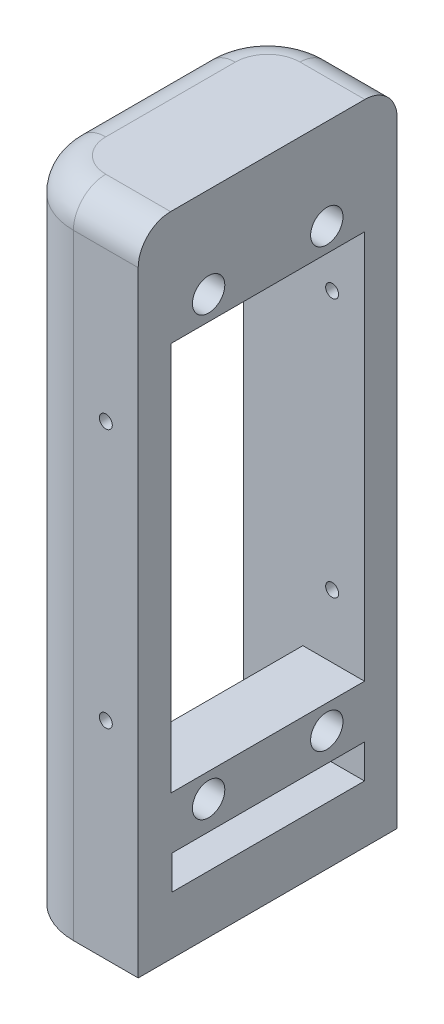
SolidWorks part; units mm, degrees
ref_plane "Front Plane" through (0, 0, 0) normal (0, 0, 1) x (1, 0, 0)
ref_plane "Top Plane" through (0, 0, 0) normal (0, 1, 0) x (1, 0, 0)
ref_plane "Right Plane" through (0, 0, 0) normal (1, 0, 0) x (0, 0, -1)
sketch "Sketch1" plane through (0, 0, 0) normal (0, 1, 0) x (1, 0, 0)
  line L0 (5.9548, -0.4092) -> (5.9548, -20.4092)
  line L1 (-14.0452, 9.5908) -> (-14.0452, -10.4092)
  line L2 (5.9548, 19.5908) -> (5.9548, -0.4092)
  line L3 (-14.0452, 9.5908) -> (-14.0452, -0.4092)
  line L4 (-4.0452, 19.5908) -> (5.9548, 19.5908)
  line L5 (-4.0452, -20.4092) -> (5.9548, -20.4092)
  arc A0 (-14.0452, -10.4092) -> (-4.0452, -20.4092) centre (-4.0452, -10.4092) ccw
  arc A1 (-4.0452, 19.5908) -> (-14.0452, 9.5908) centre (-4.0452, 9.5908) ccw
  point P2 (15.9548, -0.4092)
extrude "Boss-Extrude1" add sketch "Sketch1" along normal blind 100 contours L4 A1 L1 A0 L5 L0 L2
sketch "Sketch12" plane through (0, 100, 0) normal (0, 1, 0) x (1, 0, 0)
  line L0 (5.9548, -0.4092) -> (-2.8452, -0.4092) construction
  line L1 (5.9548, 19.5908) -> (5.9548, -20.4092) construction
  line L2 (-2.8452, -0.4092) -> (-14.0452, -0.4092) construction
  line L3 (-14.0452, 9.5908) -> (-14.0452, -10.4092) construction
  dimension "D1" = 8.8
sketch "Sketch11" plane through (-14.0452, 0, 0) normal (-1, 0, 0) x (0, 0, 1)
  line L7 (-14.1408, 22.615) -> (-14.1408, 14.5)
  line L8 (-14.1408, 14.5) -> (-10.1408, 14.5)
  line L9 (-10.1408, 14.5) -> (-10.1408, 16.148)
  line L11 (-7.2908, 14.5) -> (8.1092, 14.5)
  line L14 (10.9592, 14.5) -> (14.9592, 14.5)
  line L15 (14.9592, 14.5) -> (14.9592, 22.615)
  line L20 (14.9592, 81.925) -> (14.9592, 90)
  line L21 (14.9592, 90) -> (10.9592, 90)
  line L24 (8.1092, 90) -> (-7.2908, 90)
  line L27 (-10.1408, 90) -> (-14.1408, 90)
  line L28 (-14.1408, 90) -> (-14.1408, 81.925)
  line L32 (-14.1408, 81.925) -> (-14.1408, 80.015)
  line L33 (14.9592, 80.015) -> (14.9592, 81.925)
  line L35 (-14.1408, 38.515) -> (-14.1408, 22.615)
  line L37 (14.9592, 22.615) -> (14.9592, 38.515)
  line L42 (-14.1408, 80.015) -> (-14.1408, 38.515)
  line L46 (14.9592, 38.515) -> (14.9592, 80.015)
  line L47 (0.4092, 100) -> (0.4092, 90) construction
  line L48 (-9.5908, 100) -> (10.4092, 100) construction
  line L49 (-9.5908, 0) -> (10.4092, 0) construction
  line L50 (0.4092, 100) -> (0.4092, 90)
  line L51 (14.9592, 90) -> (-14.1408, 90)
  line L52 (14.9592, 90) -> (14.9592, 14.5)
  line L53 (-14.1408, 90) -> (-14.1408, 14.5)
  line L54 (14.9592, 14.5) -> (-14.1408, 14.5)
  line L56 (0.4092, 14.5) -> (0.4092, 0) construction
  dimension "D1" = 10
extrude "Cut-Extrude1" cut sketch "Sketch11" against normal blind 11.2
sketch "Sketch13" plane through (-2.8452, 0, 0) normal (-1, 0, 0) x (0, 0, 1)
  line L0 (14.9592, 22.615) -> (4.2292, 22.615)
  line L1 (4.2292, 22.615) -> (4.2292, 19.65)
  line L2 (2.5592, 19.65) -> (2.5592, 22.615)
  line L3 (2.5592, 22.615) -> (-1.7408, 22.615)
  line L4 (-1.7408, 22.615) -> (-1.7408, 19.65)
  line L5 (-3.4108, 19.65) -> (-3.4108, 22.615)
  line L6 (-3.4108, 22.615) -> (-14.1408, 22.615)
  line L7 (-14.1408, 22.615) -> (-14.1408, 14.5)
  line L8 (-14.1408, 14.5) -> (-10.1408, 14.5)
  line L9 (-10.1408, 14.5) -> (-10.1408, 16.148)
  line L10 (-7.2908, 16.148) -> (-7.2908, 14.5)
  line L11 (-7.2908, 14.5) -> (8.1092, 14.5)
  line L12 (8.1092, 14.5) -> (8.1092, 16.148)
  line L13 (10.9592, 16.148) -> (10.9592, 14.5)
  line L14 (10.9592, 14.5) -> (14.9592, 14.5)
  line L15 (14.9592, 14.5) -> (14.9592, 22.615)
  line L16 (-1.7408, 81.925) -> (2.5592, 81.925)
  line L17 (2.5592, 81.925) -> (2.5592, 84.85)
  line L18 (4.2292, 84.85) -> (4.2292, 81.925)
  line L19 (4.2292, 81.925) -> (14.9592, 81.925)
  line L20 (14.9592, 81.925) -> (14.9592, 90)
  line L21 (14.9592, 90) -> (10.9592, 90)
  line L22 (10.9592, 90) -> (10.9592, 88.352)
  line L23 (8.1092, 88.352) -> (8.1092, 90)
  line L24 (8.1092, 90) -> (-7.2908, 90)
  line L25 (-7.2908, 90) -> (-7.2908, 88.352)
  line L26 (-10.1408, 88.352) -> (-10.1408, 90)
  line L27 (-10.1408, 90) -> (-14.1408, 90)
  line L28 (-14.1408, 90) -> (-14.1408, 81.925)
  line L29 (-14.1408, 81.925) -> (-3.4108, 81.925)
  line L30 (-3.4108, 81.925) -> (-3.4108, 84.85)
  line L31 (-1.7408, 84.85) -> (-1.7408, 81.925)
  line L32 (-14.1408, 81.925) -> (-14.1408, 80.015)
  line L33 (14.9592, 80.015) -> (14.9592, 81.925)
  line L34 (14.9592, 81.925) -> (-14.1408, 81.925)
  line L35 (-14.1408, 38.515) -> (-14.1408, 22.615)
  line L36 (-14.1408, 22.615) -> (14.9592, 22.615)
  line L37 (14.9592, 22.615) -> (14.9592, 38.515)
  line L38 (12.9842, 38.515) -> (12.9842, 24.115)
  line L39 (12.9842, 24.115) -> (-12.1658, 24.115)
  line L40 (-12.1658, 24.115) -> (-12.1658, 38.515)
  line L41 (6.3592, 46.155) -> (-5.5408, 46.155)
  line L42 (-14.1408, 80.015) -> (-14.1408, 38.515)
  line L43 (-12.1658, 38.515) -> (-12.1658, 43.815)
  line L44 (-12.1658, 43.815) -> (12.9842, 43.815)
  line L45 (12.9842, 43.815) -> (12.9842, 38.515)
  line L46 (14.9592, 38.515) -> (14.9592, 80.015)
  line L51 (-14.1408, 14.5) -> (14.9592, 14.5)
  line L52 (14.9592, 14.5) -> (14.9592, 90)
  line L53 (14.9592, 90) -> (-14.1408, 90)
  line L54 (-14.1408, 90) -> (-14.1408, 14.5)
  line L55 (-14.1408, 14.5) -> (14.9592, 14.5)
  line L56 (14.9592, 14.5) -> (14.9592, 90)
  line L57 (14.9592, 90) -> (-14.1408, 90)
  line L58 (-14.1408, 90) -> (-14.1408, 14.5)
  arc A0 (2.5592, 19.65) -> (4.2292, 19.65) centre (3.3942, 19.65) ccw
  arc A1 (-3.4108, 19.65) -> (-1.7408, 19.65) centre (-2.5758, 19.65) ccw
  arc A2 (-7.2908, 16.148) -> (-10.1408, 16.148) centre (-8.7158, 18.5) ccw
  arc A3 (10.9592, 16.148) -> (8.1092, 16.148) centre (9.5342, 18.5) ccw
  arc A4 (4.2292, 84.85) -> (2.5592, 84.85) centre (3.3942, 84.85) ccw
  arc A5 (8.1092, 88.352) -> (10.9592, 88.352) centre (9.5342, 86) ccw
  arc A6 (-10.1408, 88.352) -> (-7.2908, 88.352) centre (-8.7158, 86) ccw
  arc A7 (-1.7408, 84.85) -> (-3.4108, 84.85) centre (-2.5758, 84.85) ccw
  circle A8 centre (0.4092, 68.825) radius 4.4
  arc A9 (9.5265, 62.3373) -> (0.4092, 80.015) centre (0.4092, 68.825) ccw
  arc A10 (9.5265, 62.3373) -> (7.9899, 59.0322) centre (17.6742, 56.5395) ccw
  arc A11 (7.9899, 59.0322) -> (6.3592, 46.155) centre (58.0182, 46.155) ccw
  arc A12 (-5.5408, 46.155) -> (-7.1715, 59.0322) centre (-57.1998, 46.155) ccw
  arc A13 (-7.1715, 59.0322) -> (-8.7081, 62.3373) centre (-16.8558, 56.5395) ccw
  arc A14 (0.4092, 80.015) -> (-8.7081, 62.3373) centre (0.4092, 68.825) ccw
  circle A15 centre (9.5342, 86) radius 2.75
  circle A16 centre (-8.7158, 86) radius 2.75
  circle A17 centre (9.5342, 18.5) radius 2.75
  circle A18 centre (-8.7158, 18.5) radius 2.75
  line M6 (14.9592, 14.5) -> (14.9592, 90)
  line M8 (-14.1408, 90) -> (-14.1408, 14.5)
  dimension "D1" = 0
extrude "Cut-Extrude5" cut sketch "Sketch13" against normal blind 22.2 contours A5 A15 | A6 A16 | A9 A14 A13 A12 L41 A11 A10 A8 | L6 L36 L3 L0 L19 L34 L16 L29 A14 A9 A10 A11 L41 A12 A13 L44 L45 L38 L39 L40 L43 M6 M8 | A8 | L45 L44 L43 L40 L39 L38 | A3 A17 | A2 A18
fillet "Fillet1" radius 5 5 edges at (0.9548, 100, -19.5908) (-11.1163, 100, -16.6619) (-14.0452, 100, 0.4092) (-11.1163, 100, 17.4803) (0.9548, 100, 20.4092)
sketch "Sketch14" plane through (-2.8452, 0, 0) normal (-1, 0, 0) x (0, 0, 1)
  line L0 (14.9592, 14.5) -> (14.9592, 22.615) construction
  line L1 (14.9592, 22.615) -> (-14.1408, 22.615) construction
  line L2 (-14.1408, 22.615) -> (-14.1408, 14.5) construction
  line L3 (-14.1408, 14.5) -> (14.9592, 14.5) construction
  line L4 (-14.1408, 90) -> (-14.1408, 81.925) construction
  line L5 (-14.1408, 81.925) -> (14.9592, 81.925) construction
  line L6 (14.9592, 81.925) -> (14.9592, 90) construction
  line L7 (14.9592, 90) -> (-14.1408, 90) construction
  line L8 (14.9592, 14.5) -> (14.9592, 22.615)
  line L9 (14.9592, 22.615) -> (-14.1408, 22.615)
  line L10 (-14.1408, 22.615) -> (-14.1408, 14.5)
  line L11 (-14.1408, 14.5) -> (14.9592, 14.5)
  line L12 (-14.1408, 90) -> (-14.1408, 81.925)
  line L13 (-14.1408, 81.925) -> (14.9592, 81.925)
  line L14 (14.9592, 81.925) -> (14.9592, 90)
  line L15 (14.9592, 90) -> (-14.1408, 90)
  circle A0 centre (9.5342, 18.5) radius 2.75 construction
  circle A1 centre (-8.7158, 18.5) radius 2.75 construction
  circle A2 centre (9.5342, 86) radius 2.75 construction
  circle A3 centre (-8.7158, 86) radius 2.75 construction
  circle A4 centre (9.5342, 18.5) radius 2.75
  circle A5 centre (-8.7158, 18.5) radius 2.75
  circle A6 centre (9.5342, 86) radius 2.75
  circle A7 centre (-8.7158, 86) radius 2.75
extrude "Boss-Extrude2" add sketch "Sketch14" along normal blind 0.72
sketch "Sketch15" plane through (5.9548, 0, 0) normal (1, 0, 0) x (0, 0, -1)
  circle A0 centre (8.7158, 18.5) radius 1.25
  circle A1 centre (8.7158, 18.5) radius 2.75
  circle A2 centre (8.7158, 18.5) radius 2.75
  circle A3 centre (-9.5342, 18.5) radius 2.75
  circle A4 centre (-9.5342, 18.5) radius 2.75
  circle A5 centre (8.7158, 86) radius 2.75
  circle A6 centre (8.7158, 86) radius 2.75
  circle A7 centre (-9.5342, 86) radius 2.75
  circle A8 centre (-9.5342, 86) radius 2.75
  circle A9 centre (-9.5342, 18.5) radius 1.25
  circle A10 centre (8.7158, 86) radius 1.25
  circle A11 centre (-9.5342, 86) radius 1.25
  dimension "D5" = 1.5
  dimension "D1" = 0
  dimension "D2" = 0
  dimension "D3" = 0
  dimension "D4" = 0
extrude "Boss-Extrude3" add sketch "Sketch15" against normal up to surface (9.52 mm away) up to face at (-3.5652, 18.5, 12.2842)
sketch "Sketch16" plane through (5.9548, 0, 0) normal (1, 0, 0) x (0, 0, -1)
  circle A0 centre (-9.5342, 18.5) radius 2.5
  circle A1 centre (8.7158, 18.5) radius 2.5
  circle A2 centre (-9.5342, 86) radius 2.5
  circle A3 centre (8.7158, 86) radius 2.5
  dimension "D1" = 5
  dimension "D2" = 5
  dimension "D3" = 5
  dimension "D4" = 5
extrude "Cut-Extrude6" cut sketch "Sketch16" against normal blind 4
sketch "Sketch17" plane through (-3.5652, 0, 0) normal (-1, 0, 0) x (0, 0, 1)
  line L0 (-14.1408, 90) -> (-14.1408, 14.5)
  line L1 (-14.1408, 90) -> (14.8232, 90)
  line L2 (-14.1408, 14.5) -> (14.8232, 14.5)
  line L3 (14.8232, 90) -> (14.8232, 14.5)
  line L4 (-14.5408, 90.4) -> (-14.5408, 14.1)
  line L5 (-14.5408, 14.1) -> (15.2232, 14.1)
  line L6 (15.2232, 90.4) -> (15.2232, 14.1)
  line L7 (-14.5408, 90.4) -> (15.2232, 90.4)
  dimension "D1" = 0.4
extrude "Cut-Extrude7" cut sketch "Sketch17" along normal blind 44
sketch "Sketch18" plane through (-3.5652, 0, 0) normal (-1, 0, 0) x (0, 0, 1)
  line L0 (-14.1408, 81.925) -> (-14.1408, 22.615) construction
  line L1 (14.9592, 22.615) -> (-14.1408, 22.615) construction
  line L2 (14.9592, 22.615) -> (14.9592, 81.925) construction
  line L3 (-14.1408, 81.925) -> (14.9592, 81.925) construction
  line L4 (-14.1408, 81.925) -> (-14.1408, 22.615)
  line L5 (14.9592, 22.615) -> (-14.1408, 22.615)
  line L6 (14.9592, 22.615) -> (14.9592, 81.925)
  line L7 (-14.1408, 81.925) -> (14.9592, 81.925)
  line L8 (-14.5408, 82.325) -> (-14.5408, 22.215)
  line L9 (15.3592, 22.215) -> (-14.5408, 22.215)
  line L10 (15.3592, 22.215) -> (15.3592, 82.325)
  line L11 (-14.5408, 82.325) -> (15.3592, 82.325)
  dimension "D1" = 0.4
extrude "Cut-Extrude8" cut sketch "Sketch18" against normal blind 44
sketch "Sketch19" plane through (-14.0452, 0, 0) normal (-1, 0, 0) x (0, 0, 1)
  line L0 (-14.5408, 14.1) -> (15.2232, 14.1)
  line L1 (-14.5408, 14.1) -> (-14.5408, 8.8734)
  line L2 (15.2232, 14.1) -> (15.2232, 8.8734)
  line L3 (-14.5408, 8.8734) -> (15.2232, 8.8734)
extrude "Cut-Extrude9" cut sketch "Sketch19" against normal blind 44
sketch "Sketch21" plane through (0, 0, -19.5908) normal (0, 0, -1) x (-1, 0, 0)
  line L0 (-5.9548, 8.8734) -> (12.8102, 8.8734) construction
  line L1 (-5.9548, 8.8734) -> (12.8102, 8.8734)
  line L2 (12.8102, 90.4) -> (3.5652, 90.4) construction
  line L3 (12.8102, 90.4) -> (3.5652, 90.4)
  line L4 (-5.9548, 95) -> (-5.9548, 8.8734) construction
  line L5 (4.0452, 95) -> (-5.9548, 95) construction
  line L6 (-5.9548, 51.9367) -> (4.0452, 51.9367) construction
  line L7 (4.0452, 95) -> (4.0452, 0) construction
  line L8 (-5.9548, 95) -> (-5.9548, 0) construction
  line L9 (-0.9548, 51.9367) -> (-0.9548, 31.9367) construction
  line L10 (-0.9548, 51.9367) -> (-0.9548, 71.9367) construction
  circle A0 centre (-0.9548, 71.9367) radius 1
  circle A1 centre (-0.9548, 31.9367) radius 1
  dimension "D3" = 2
  dimension "2" = 2
  dimension "D1" = 20
  dimension "D2" = 20
extrude "Cut-Extrude10" cut sketch "Sketch21" against normal blind 122.5 contours A0 | A1
sketch "Sketch22" plane through (0, 0, 0) normal (0, -1, 0) x (1, 0, 0)
  line L0 (-4.0452, -19.5908) -> (5.9548, -19.5908)
  line L2 (5.9548, 20.4092) -> (-4.0452, 20.4092)
  circle A0 centre (-4.0452, 10.4092) radius 1
  circle A1 centre (-4.0452, -9.5908) radius 1
  arc A2 (-4.0452, 20.4092) -> (-14.0452, 10.4092) centre (-4.0452, 10.4092) ccw
  arc A3 (-14.0452, -9.5908) -> (-4.0452, -19.5908) centre (-4.0452, -9.5908) ccw
extrude "Cut-Extrude11" cut sketch "Sketch22" against normal blind 10.5 contours A1 | A0
